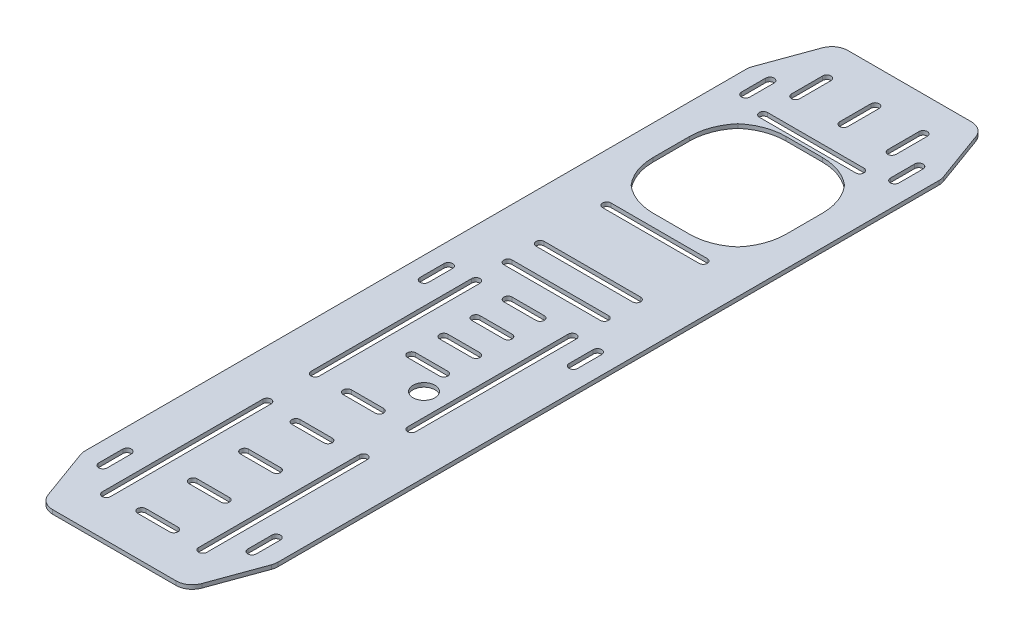
SolidWorks part; units mm, degrees
material "6061-T6 (SS)"
ref_plane "Front Plane" through (0, 0, 0) normal (0, 0, 1) x (1, 0, 0)
ref_plane "Top Plane" through (0, 0, 0) normal (0, 1, 0) x (1, 0, 0)
ref_plane "Right Plane" through (0, 0, 0) normal (1, 0, 0) x (0, 0, -1)
sketch "Sketch1" plane through (0, 0, 0) normal (0, 1, 0) x (1, 0, 0)
  line L0 (0, 495.0997) -> (0, -495.0997) construction
  line L8 (76.2, 330.2) -> (-76.2, 330.2)
  line L9 (76.2, 330.2) -> (76.2, -330.2)
  line L10 (76.2, -330.2) -> (-76.2, -330.2)
  line L11 (-76.2, 330.2) -> (-76.2, -330.2)
  line L12 (76.2, 330.2) -> (-76.2, -330.2) construction
  line L13 (76.2, -330.2) -> (-76.2, 330.2) construction
  point P7 (0, 0)
  dimension "D1" = 660.4
  dimension "D2" = 152.4
extrude "Boss-Extrude1" add sketch "Sketch1" along normal blind 3.18
sketch "Sketch5" plane through (0, 0, 0) normal (0, -1, 0) x (1, 0, 0)
  line L0 (76.2, 279.4) -> (57.7103, 330.2)
  line L1 (76.2, 330.2) -> (76.2, -330.2) construction
  line L2 (-76.2, 330.2) -> (76.2, 330.2) construction
  line L3 (57.7103, 330.2) -> (76.2, 330.2)
  line L4 (76.2, 330.2) -> (76.2, 279.4)
  line L5 (0, -1.749) -> (0, 1.749) construction
  line L6 (-57.7103, 330.2) -> (-76.2, 330.2)
  line L7 (-76.2, 279.4) -> (-57.7103, 330.2)
  line L8 (-76.2, 330.2) -> (-76.2, 279.4)
  line L9 (1.749, 0) -> (-1.749, 0) construction
  line L10 (-76.2, -279.4) -> (-57.7103, -330.2)
  line L11 (-76.2, -330.2) -> (-76.2, -279.4)
  line L12 (-57.7103, -330.2) -> (-76.2, -330.2)
  line L13 (57.7103, -330.2) -> (76.2, -330.2)
  line L14 (76.2, -279.4) -> (57.7103, -330.2)
  line L15 (76.2, -330.2) -> (76.2, -279.4)
  dimension "D1" = 20
  dimension "D2" = 50.8
sketch "Sketch3" plane through (0, 3.18, 0) normal (0, 1, 0) x (1, 0, 0)
  line L0 (-38.1, -101.6) -> (38.1, -101.6) construction
  line L1 (-76.2, -330.2) -> (76.2, -330.2) construction
  line L2 (-38.1, 50.8) -> (38.1, 50.8) construction
  line L5 (-38.1, 54.0639) -> (38.1, 54.0639)
  line L9 (-38.1, 47.5361) -> (38.1, 47.5361)
  line L12 (-76.2, 0) -> (76.2, 0) construction
  line L13 (-76.2, 330.2) -> (-76.2, -330.2) construction
  line L14 (76.2, -330.2) -> (76.2, 330.2) construction
  line L15 (-38.1, 25.4) -> (-38.1, -101.6) construction
  line L16 (-41.3639, 25.4) -> (-41.3639, -101.6)
  line L17 (-34.8361, 25.4) -> (-34.8361, -101.6)
  line L18 (38.1, 25.4) -> (38.1, -101.6) construction
  line L19 (41.3639, 25.4) -> (41.3639, -101.6)
  line L20 (34.8361, 25.4) -> (34.8361, -101.6)
  line L21 (-76.2, -38.1) -> (76.2, -38.1) construction
  line L22 (-76.2, 330.2) -> (-76.2, -330.2) construction
  line L23 (76.2, -330.2) -> (76.2, 330.2) construction
  line L24 (-38.1, -127) -> (38.1, -127) construction
  line L25 (-38.1, -130.2639) -> (38.1, -130.2639)
  line L26 (-38.1, -123.7361) -> (38.1, -123.7361)
  line L27 (-76.2, -127) -> (76.2, -127) construction
  line L28 (38.1, -279.4) -> (38.1, -152.4) construction
  line L29 (41.3639, -279.4) -> (41.3639, -152.4)
  line L30 (34.8361, -279.4) -> (34.8361, -152.4)
  line L31 (-38.1, -279.4) -> (-38.1, -152.4) construction
  line L32 (-41.3639, -279.4) -> (-41.3639, -152.4)
  line L33 (-34.8361, -279.4) -> (-34.8361, -152.4)
  line L34 (-76.2, -215.9) -> (76.2, -215.9) construction
  line L35 (-38.1, -304.8) -> (38.1, -304.8) construction
  line L36 (-38.1, -301.5361) -> (38.1, -301.5361)
  line L37 (-38.1, -308.0639) -> (38.1, -308.0639)
  line L38 (-12.7, -279.4) -> (12.7, -279.4) construction
  line L39 (-12.7, -276.1361) -> (12.7, -276.1361)
  line L40 (-12.7, -282.6639) -> (12.7, -282.6639)
  line L44 (-12.7, -228.6) -> (12.7, -228.6) construction
  line L45 (-12.7, -225.3361) -> (12.7, -225.3361)
  line L46 (-12.7, -231.8639) -> (12.7, -231.8639)
  line L47 (-12.7, -203.2) -> (12.7, -203.2) construction
  line L48 (-12.7, -199.9361) -> (12.7, -199.9361)
  line L49 (-12.7, -206.4639) -> (12.7, -206.4639)
  line L50 (-12.7, -177.8) -> (12.7, -177.8) construction
  line L51 (-12.7, -174.5361) -> (12.7, -174.5361)
  line L52 (-12.7, -181.0639) -> (12.7, -181.0639)
  line L53 (-12.7, -152.4) -> (12.7, -152.4) construction
  line L54 (-12.7, -149.1361) -> (12.7, -149.1361)
  line L55 (-12.7, -155.6639) -> (12.7, -155.6639)
  line L56 (-12.7, 25.4) -> (12.7, 25.4) construction
  line L57 (-12.7, 22.1361) -> (12.7, 22.1361)
  line L58 (-12.7, 28.6639) -> (12.7, 28.6639)
  line L59 (-12.7, 0) -> (12.7, 0) construction
  line L60 (-12.7, -3.2639) -> (12.7, -3.2639)
  line L61 (-12.7, 3.2639) -> (12.7, 3.2639)
  line L62 (-12.7, -25.4) -> (12.7, -25.4) construction
  line L63 (-12.7, -28.6639) -> (12.7, -28.6639)
  line L64 (-12.7, -22.1361) -> (12.7, -22.1361)
  line L65 (-12.7, -50.8) -> (12.7, -50.8) construction
  line L66 (-12.7, -54.0639) -> (12.7, -54.0639)
  line L67 (-12.7, -47.5361) -> (12.7, -47.5361)
  line L71 (-12.7, -101.6) -> (12.7, -101.6) construction
  line L72 (-12.7, -104.8639) -> (12.7, -104.8639)
  line L73 (-12.7, -98.3361) -> (12.7, -98.3361)
  line L74 (-76.2, 63.5) -> (76.2, 63.5) construction
  line L75 (-38.1, 76.2) -> (38.1, 76.2) construction
  line L76 (-38.1, 72.9361) -> (38.1, 72.9361)
  line L77 (-38.1, 79.4639) -> (38.1, 79.4639)
  line L78 (-76.2, 151.7678) -> (76.2, 151.7678) construction
  line L79 (76.2, 330.2) -> (-76.2, 330.2) construction
  line L80 (-38.1, 207.0156) -> (38.1, 207.0156) construction
  line L83 (-38.1, 252.7356) -> (38.1, 252.7356) construction
  line L84 (-38.1, 249.4717) -> (38.1, 249.4717)
  line L85 (-38.1, 255.9995) -> (38.1, 255.9995)
  line L86 (-38.1, 302.8393) -> (-38.1, 278.1356) construction
  line L87 (-34.8361, 302.8393) -> (-34.8361, 278.1356)
  line L88 (-41.3639, 302.8393) -> (-41.3639, 278.1356)
  line L89 (0, 302.8393) -> (0, 278.1356) construction
  line L90 (3.2639, 302.8393) -> (3.2639, 278.1356)
  line L91 (-3.2639, 302.8393) -> (-3.2639, 278.1356)
  line L92 (38.1, 302.8393) -> (38.1, 278.1356) construction
  line L93 (41.3639, 302.8393) -> (41.3639, 278.1356)
  line L94 (34.8361, 302.8393) -> (34.8361, 278.1356)
  line L95 (-38.1, 203.7517) -> (38.1, 203.7517)
  line L96 (-38.1, 210.2795) -> (38.1, 210.2795)
  line L97 (76.2, 330.2) -> (-76.2, 330.2) construction
  line L113 (-12.7, -254) -> (12.7, -254) construction
  line L114 (-12.7, -250.7361) -> (12.7, -250.7361)
  line L115 (-12.7, -257.2639) -> (12.7, -257.2639)
  line L116 (-12.7, -254) -> (12.7, -254) construction
  line L117 (-12.7, -250.7361) -> (12.7, -250.7361)
  line L118 (-12.7, -257.2639) -> (12.7, -257.2639)
  arc A4 (-41.3639, 25.4) -> (-34.8361, 25.4) centre (-38.1, 25.4) cw
  arc A5 (-34.8361, -101.6) -> (-41.3639, -101.6) centre (-38.1, -101.6) cw
  arc A6 (41.3639, 25.4) -> (34.8361, 25.4) centre (38.1, 25.4) ccw
  arc A7 (34.8361, -101.6) -> (41.3639, -101.6) centre (38.1, -101.6) ccw
  arc A8 (-38.1, 54.0639) -> (-38.1, 47.5361) centre (-38.1, 50.8) ccw
  arc A9 (38.1, 47.5361) -> (38.1, 54.0639) centre (38.1, 50.8) ccw
  arc A10 (-38.1, -130.2639) -> (-38.1, -123.7361) centre (-38.1, -127) cw
  arc A11 (38.1, -123.7361) -> (38.1, -130.2639) centre (38.1, -127) cw
  arc A12 (41.3639, -279.4) -> (34.8361, -279.4) centre (38.1, -279.4) cw
  arc A13 (34.8361, -152.4) -> (41.3639, -152.4) centre (38.1, -152.4) cw
  arc A14 (-41.3639, -279.4) -> (-34.8361, -279.4) centre (-38.1, -279.4) ccw
  arc A15 (-34.8361, -152.4) -> (-41.3639, -152.4) centre (-38.1, -152.4) ccw
  arc A16 (-38.1, -301.5361) -> (-38.1, -308.0639) centre (-38.1, -304.8) ccw
  arc A17 (38.1, -308.0639) -> (38.1, -301.5361) centre (38.1, -304.8) ccw
  arc A18 (-12.7, -276.1361) -> (-12.7, -282.6639) centre (-12.7, -279.4) ccw
  arc A19 (12.7, -282.6639) -> (12.7, -276.1361) centre (12.7, -279.4) ccw
  arc A22 (-12.7, -225.3361) -> (-12.7, -231.8639) centre (-12.7, -228.6) ccw
  arc A23 (12.7, -231.8639) -> (12.7, -225.3361) centre (12.7, -228.6) ccw
  arc A24 (-12.7, -199.9361) -> (-12.7, -206.4639) centre (-12.7, -203.2) ccw
  arc A25 (12.7, -206.4639) -> (12.7, -199.9361) centre (12.7, -203.2) ccw
  arc A26 (-12.7, -174.5361) -> (-12.7, -181.0639) centre (-12.7, -177.8) ccw
  arc A27 (12.7, -181.0639) -> (12.7, -174.5361) centre (12.7, -177.8) ccw
  arc A28 (-12.7, -149.1361) -> (-12.7, -155.6639) centre (-12.7, -152.4) ccw
  arc A29 (12.7, -155.6639) -> (12.7, -149.1361) centre (12.7, -152.4) ccw
  arc A30 (-12.7, 22.1361) -> (-12.7, 28.6639) centre (-12.7, 25.4) cw
  arc A31 (12.7, 28.6639) -> (12.7, 22.1361) centre (12.7, 25.4) cw
  arc A32 (-12.7, -3.2639) -> (-12.7, 3.2639) centre (-12.7, 0) cw
  arc A33 (12.7, 3.2639) -> (12.7, -3.2639) centre (12.7, 0) cw
  arc A34 (-12.7, -28.6639) -> (-12.7, -22.1361) centre (-12.7, -25.4) cw
  arc A35 (12.7, -22.1361) -> (12.7, -28.6639) centre (12.7, -25.4) cw
  arc A36 (-12.7, -54.0639) -> (-12.7, -47.5361) centre (-12.7, -50.8) cw
  arc A37 (12.7, -47.5361) -> (12.7, -54.0639) centre (12.7, -50.8) cw
  arc A40 (-12.7, -104.8639) -> (-12.7, -98.3361) centre (-12.7, -101.6) cw
  arc A41 (12.7, -98.3361) -> (12.7, -104.8639) centre (12.7, -101.6) cw
  arc A42 (-38.1, 72.9361) -> (-38.1, 79.4639) centre (-38.1, 76.2) cw
  arc A43 (38.1, 79.4639) -> (38.1, 72.9361) centre (38.1, 76.2) cw
  arc A46 (-38.1, 249.4717) -> (-38.1, 255.9995) centre (-38.1, 252.7356) cw
  arc A47 (38.1, 255.9995) -> (38.1, 249.4717) centre (38.1, 252.7356) cw
  arc A48 (-34.8361, 302.8393) -> (-41.3639, 302.8393) centre (-38.1, 302.8393) ccw
  arc A49 (-41.3639, 278.1356) -> (-34.8361, 278.1356) centre (-38.1, 278.1356) ccw
  arc A50 (3.2639, 302.8393) -> (-3.2639, 302.8393) centre (0, 302.8393) ccw
  arc A51 (-3.2639, 278.1356) -> (3.2639, 278.1356) centre (0, 278.1356) ccw
  arc A52 (41.3639, 302.8393) -> (34.8361, 302.8393) centre (38.1, 302.8393) ccw
  arc A53 (34.8361, 278.1356) -> (41.3639, 278.1356) centre (38.1, 278.1356) ccw
  arc A54 (-38.1, 203.7517) -> (-38.1, 210.2795) centre (-38.1, 207.0156) cw
  arc A55 (38.1, 210.2795) -> (38.1, 203.7517) centre (38.1, 207.0156) cw
  arc A68 (-12.7, -250.7361) -> (-12.7, -257.2639) centre (-12.7, -254) ccw
  arc A69 (12.7, -257.2639) -> (12.7, -250.7361) centre (12.7, -254) ccw
  point P2 (0, 50.8)
  point P26 (0, -127)
  point P36 (-38.1, -38.1)
  point P43 (38.1, -38.1)
  point P55 (38.1, -215.9)
  point P62 (-38.1, -215.9)
  point P71 (0, -304.8)
  point P78 (0, -279.4)
  point P94 (0, -228.6)
  point P101 (0, -203.2)
  point P108 (0, -177.8)
  point P115 (0, -152.4)
  point P121 (0, 25.4)
  point P128 (0, 0)
  point P135 (0, -25.4)
  point P142 (0, -50.8)
  point P156 (0, -101.6)
  point P165 (0, 76.2)
  point P176 (0, 207.0156)
  point P177 (0, 207.0156)
  point P183 (0, 252.7356)
  point P190 (-38.1, 290.4874)
  point P197 (0, 290.4874)
  point P205 (38.1, 290.4874)
  point P212 (0, -254)
  point P221 (0, -254)
  point P228 (0, -254)
  point P235 (0, -254)
  point P242 (0, -254)
  point P249 (0, -254)
  point P256 (0, -254)
  dimension "D1" = 3.2639
  dimension "D2" = 76.2
  dimension "D5" = 3.2639
  dimension "D7" = 3.2639
  dimension "D14" = 3.2639
  dimension "D3" = 228.6
  dimension "D4" = 127
  dimension "D6" = 25.4
  dimension "D8" = 25.4
  dimension "D9" = 6
  dimension "D11" = 12.7
  dimension "D12" = 50.1037
  dimension "7.02489" = 178.4322
  dimension "D13" = 25.4
  dimension "D16" = 38.1
  dimension "D17" = 123.1844
  dimension "D15" = 3
extrude "Cut-Extrude2" cut sketch "Sketch3" against normal through all
sketch "Sketch4" plane through (0, 3.18, 0) normal (0, 1, 0) x (1, 0, 0)
  line L47 (-14.3614, 141.82) -> (14.3614, 141.82)
  line L48 (52.54, 179.9986) -> (52.54, 208.7214)
  line L49 (14.3614, 246.9) -> (-14.3614, 246.9)
  line L50 (-52.54, 208.7214) -> (-52.54, 179.9986)
  line L51 (-14.3614, 141.82) -> (14.3614, 141.82)
  line L52 (52.54, 179.9986) -> (52.54, 208.7214)
  line L53 (14.3614, 246.9) -> (-14.3614, 246.9)
  line L54 (-52.54, 208.7214) -> (-52.54, 179.9986)
  arc A93 (-42.1819, 152.1781) -> (-14.3614, 141.82) centre (-14.3614, 184.36) ccw
  arc A94 (14.3614, 141.82) -> (42.1819, 152.1781) centre (14.3614, 184.36) ccw
  arc A95 (42.1819, 152.1781) -> (52.54, 179.9986) centre (10, 179.9986) ccw
  arc A96 (52.54, 208.7214) -> (42.1819, 236.5419) centre (10, 208.7214) ccw
  arc A97 (42.1819, 236.5419) -> (14.3614, 246.9) centre (14.3614, 204.36) ccw
  arc A98 (-14.3614, 246.9) -> (-42.1819, 236.5419) centre (-14.3614, 204.36) ccw
  arc A99 (-42.1819, 236.5419) -> (-52.54, 208.7214) centre (-10, 208.7214) ccw
  arc A100 (-52.54, 179.9986) -> (-42.1819, 152.1781) centre (-10, 179.9986) ccw
  arc A101 (-42.1819, 152.1781) -> (-14.3614, 141.82) centre (-14.3614, 184.36) ccw
  arc A102 (14.3614, 141.82) -> (42.1819, 152.1781) centre (14.3614, 184.36) ccw
  arc A103 (42.1819, 152.1781) -> (52.54, 179.9986) centre (10, 179.9986) ccw
  arc A104 (52.54, 208.7214) -> (42.1819, 236.5419) centre (10, 208.7214) ccw
  arc A105 (42.1819, 236.5419) -> (14.3614, 246.9) centre (14.3614, 204.36) ccw
  arc A106 (-14.3614, 246.9) -> (-42.1819, 236.5419) centre (-14.3614, 204.36) ccw
  arc A107 (-42.1819, 236.5419) -> (-52.54, 208.7214) centre (-10, 208.7214) ccw
  arc A108 (-52.54, 179.9986) -> (-42.1819, 152.1781) centre (-10, 179.9986) ccw
  dimension "D1" = 2.54
extrude "Cut-Extrude3" cut sketch "Sketch4" against normal through all
extrude "Cut-Extrude4" cut sketch "Sketch5" against normal through all
fillet "Fillet1" radius 12.7 8 edges at (-76.2, 1.59, -279.4) (-57.7103, 1.59, -330.2) (57.7103, 1.59, -330.2) (76.2, 1.59, -279.4) (76.2, 1.59, 279.4) (57.7103, 1.59, 330.2) (-57.7103, 1.59, 330.2) (-76.2, 1.59, 279.4)
sketch "Sketch6" plane through (0, 3.18, 0) normal (0, 1, 0) x (1, 0, 0)
  circle A1 centre (17.106, -70.8034) radius 8.636 construction
  circle A2 centre (17.106, -70.8034) radius 8.636
sketch "Sketch7" plane through (0, 0, 0) normal (0, -1, 0) x (1, 0, 0)
  line L0 (76.2, 330.2) -> (76.2, 120.65)
  line L1 (76.2, 277.1606) -> (76.2, -277.1606) construction
  line L2 (76.2, 120.65) -> (-76.2, 120.65)
  line L3 (-76.2, 120.65) -> (-76.2, 330.2)
  line L4 (-76.2, -277.1606) -> (-76.2, 277.1606) construction
  line L5 (-76.2, 330.2) -> (76.2, 330.2)
  line L6 (-48.8177, 330.2) -> (48.8177, 330.2) construction
  dimension "D1" = 209.55
extrude "Cut-Extrude6" cut sketch "Sketch7" against normal up to next
sketch "Sketch8" plane through (0, 0, 0) normal (0, -1, 0) x (1, 0, 0)
  line L0 (76.2, 69.85) -> (76.2, 120.65)
  line L1 (76.2, 120.65) -> (76.2, -277.1606) construction
  line L2 (76.2, 120.65) -> (57.7103, 120.65)
  line L3 (-76.2, 120.65) -> (76.2, 120.65) construction
  line L4 (57.7103, 120.65) -> (76.2, 69.85)
  line L5 (0, -330.2) -> (0, 120.65) construction
  line L6 (48.8177, -330.2) -> (-48.8177, -330.2) construction
  line L7 (-76.2, 120.65) -> (-57.7103, 120.65)
  line L8 (-76.2, 69.85) -> (-76.2, 120.65)
  line L9 (-57.7103, 120.65) -> (-76.2, 69.85)
  dimension "D1" = 50.8
  dimension "D2" = 20
sketch "Sketch9" plane through (0, 0, 0) normal (0, -1, 0) x (1, 0, 0)
  line L0 (58.674, -259.715) -> (58.674, -278.765) construction
  line L1 (62.0522, -259.715) -> (62.0522, -278.765)
  line L2 (55.2958, -259.715) -> (55.2958, -278.765)
  line L3 (-59.0358, -259.715) -> (-59.0358, -278.765) construction
  line L4 (-55.6576, -259.715) -> (-55.6576, -278.765)
  line L5 (-62.414, -259.715) -> (-62.414, -278.765)
  line L6 (-59.182, -259.715) -> (-59.182, -278.765) construction
  line L7 (76.2, 120.65) -> (76.2, -277.1606) construction
  line L8 (-76.2, -277.1606) -> (-76.2, 120.65) construction
  line L9 (-55.8038, -259.715) -> (-55.8038, -278.765)
  line L15 (58.674, -269.24) -> (-59.0358, -269.24) construction
  line L16 (48.8177, -330.2) -> (-48.8177, -330.2) construction
  line L18 (-62.5602, -259.715) -> (-62.5602, -278.765)
  line L21 (0, 120.65) -> (0, 171.45) construction
  line L22 (0, -330.2) -> (0, 171.45) construction
  line L23 (-59.182, -5.715) -> (-59.182, -24.765) construction
  line L24 (-55.8038, -5.715) -> (-55.8038, -24.765)
  line L25 (-62.5602, -5.715) -> (-62.5602, -24.765)
  line L26 (-59.182, 248.285) -> (-59.182, 229.235) construction
  line L27 (-55.8038, 248.285) -> (-55.8038, 229.235)
  line L28 (-62.5602, 248.285) -> (-62.5602, 229.235)
  line L29 (58.674, -5.715) -> (58.674, -24.765) construction
  line L30 (62.0522, -5.715) -> (62.0522, -24.765)
  line L31 (55.2958, -5.715) -> (55.2958, -24.765)
  line L32 (58.674, 248.285) -> (58.674, 229.235) construction
  line L33 (62.0522, 248.285) -> (62.0522, 229.235)
  line L34 (55.2958, 248.285) -> (55.2958, 229.235)
  arc A0 (62.0522, -259.715) -> (55.2958, -259.715) centre (58.674, -259.715) ccw
  arc A1 (55.2958, -278.765) -> (62.0522, -278.765) centre (58.674, -278.765) ccw
  arc A3 (-55.6576, -259.715) -> (-62.414, -259.715) centre (-59.0358, -259.715) ccw
  arc A4 (-62.414, -278.765) -> (-55.6576, -278.765) centre (-59.0358, -278.765) ccw
  arc A12 (-55.8038, -259.715) -> (-62.5602, -259.715) centre (-59.182, -259.715) ccw
  arc A13 (-62.5602, -278.765) -> (-55.8038, -278.765) centre (-59.182, -278.765) ccw
  arc A14 (-55.8038, -5.715) -> (-62.5602, -5.715) centre (-59.182, -5.715) ccw
  arc A15 (-62.5602, -24.765) -> (-55.8038, -24.765) centre (-59.182, -24.765) ccw
  arc A16 (-55.8038, 248.285) -> (-62.5602, 248.285) centre (-59.182, 248.285) ccw
  arc A17 (-62.5602, 229.235) -> (-55.8038, 229.235) centre (-59.182, 229.235) ccw
  arc A18 (62.0522, -5.715) -> (55.2958, -5.715) centre (58.674, -5.715) ccw
  arc A19 (55.2958, -24.765) -> (62.0522, -24.765) centre (58.674, -24.765) ccw
  arc A20 (62.0522, 248.285) -> (55.2958, 248.285) centre (58.674, 248.285) ccw
  arc A21 (55.2958, 229.235) -> (62.0522, 229.235) centre (58.674, 229.235) ccw
  point P3 (58.674, -269.24)
  point P13 (-59.0358, -269.24)
  point P19 (0, 0)
  point P20 (0, 0)
  point P21 (0, 0)
  point P28 (-59.182, -269.24)
  point P35 (-59.182, -15.24)
  point P42 (-59.182, 238.76)
  point P54 (58.674, -15.24)
  point P61 (58.674, 238.76)
  point P66 (0, 0)
  point P67 (0, 0)
  dimension "D2" = 3.3782
  dimension "D1" = 19.05
  dimension "D3" = 60.96
  dimension "D4" = 17.1642
  dimension "D5" = 17.526
  dimension "D6" = 50.8
  dimension "D7" = 2
  dimension "D8" = 3
extrude "Cut-Extrude9" cut sketch "Sketch6" against normal through all
sketch "Sketch10" plane through (0, 0, 0) normal (0, -1, 0) x (1, 0, 0)
  line L0 (-38.1, -252.7356) -> (-38.1, -103.0796) construction
  line L3 (38.1, -252.7356) -> (38.1, -103.0796) construction
  line L4 (-38.1, -128.9041) -> (38.1, -128.9041) construction
  line L5 (-38.1, -128.9041) -> (38.1, -128.9041) construction
  line L6 (-38.1, -125.6402) -> (38.1, -125.6402)
  line L7 (-38.1, -132.168) -> (38.1, -132.168)
  line L8 (-14.3614, -141.82) -> (14.3614, -141.82) construction
  arc A2 (-38.1, -125.6402) -> (-38.1, -132.168) centre (-38.1, -128.9041) ccw
  arc A3 (38.1, -132.168) -> (38.1, -125.6402) centre (38.1, -128.9041) ccw
  arc A4 (-38.1, -249.4717) -> (-38.1, -255.9995) centre (-38.1, -252.7356) ccw construction
  point P4 (-0.038, -128.9041)
  point P9 (0, -128.9041)
  dimension "D1" = 9.652
extrude "Cut-Extrude10" cut sketch "Sketch10" against normal through all
sketch "Sketch11" plane through (0, 0, 120.65) normal (0, 0, 1) x (1, 0, 0)
  line L0 (-75.4341, 3.18) -> (76.2, 3.18)
  line L1 (76.2, 3.18) -> (76.2, 0)
  line L2 (76.2, 0) -> (-76.2, 0)
  line L3 (-76.2, 0) -> (-76.2, 3.18)
  line L4 (-76.2, 3.18) -> (-75.4341, 3.18)
extrude "Boss-Extrude2" add sketch "Sketch11" along normal blind 177.8
sketch "Sketch12" plane through (0, 0, 0) normal (0, -1, 0) x (1, 0, 0)
  line L0 (76.2, 298.45) -> (76.2, 247.65)
  line L1 (76.2, 298.45) -> (76.2, -277.1606) construction
  line L2 (76.2, 247.65) -> (57.7103, 298.45)
  line L3 (-76.2, 298.45) -> (76.2, 298.45) construction
  line L4 (57.7103, 298.45) -> (76.2, 298.45)
  line L5 (-76.2, 298.45) -> (-76.2, 247.65)
  line L6 (-76.2, -277.1606) -> (-76.2, 298.45) construction
  line L7 (-76.2, 247.65) -> (-57.7103, 298.45)
  line L8 (-57.7103, 298.45) -> (-76.2, 298.45)
  dimension "D1" = 20
  dimension "D2" = 50.8
  dimension "D3" = 20
  dimension "D4" = 50.8
extrude "Cut-Extrude11" cut sketch "Sketch12" against normal blind 177.8
fillet "Fillet2" radius 12.7 4 edges at (-57.7103, 1.59, 298.45) (-76.2, 1.59, 247.65) (57.7103, 1.59, 298.45) (76.2, 1.59, 247.65)
sketch "Sketch13" plane through (0, 0, 0) normal (0, -1, 0) x (1, 0, 0)
  line L0 (-55.8038, 248.285) -> (-55.8038, 229.235) construction
  line L1 (-55.8038, 248.285) -> (-55.8038, 229.235)
  line L2 (62.0522, -259.715) -> (62.0522, -278.765) construction
  line L3 (-62.414, -259.715) -> (-62.414, -278.765) construction
  line L4 (-55.8038, -5.715) -> (-55.8038, -24.765) construction
  line L5 (62.0522, -5.715) -> (62.0522, -24.765) construction
  line L6 (55.2958, 248.285) -> (55.2958, 229.235) construction
  line L7 (62.0522, -259.715) -> (62.0522, -278.765)
  line L8 (-62.414, -259.715) -> (-62.414, -278.765)
  line L9 (-55.8038, -5.715) -> (-55.8038, -24.765)
  line L10 (62.0522, -5.715) -> (62.0522, -24.765)
  line L11 (55.2958, 248.285) -> (55.2958, 229.235)
  line L12 (55.2958, -259.715) -> (55.2958, -278.765) construction
  line L13 (-55.6576, -259.715) -> (-55.6576, -278.765) construction
  line L14 (-62.5602, -5.715) -> (-62.5602, -24.765) construction
  line L15 (55.2958, -5.715) -> (55.2958, -24.765) construction
  line L16 (-62.5602, 248.285) -> (-62.5602, 229.235) construction
  line L17 (55.2958, -259.715) -> (55.2958, -278.765)
  line L18 (-55.6576, -259.715) -> (-55.6576, -278.765)
  line L19 (-62.5602, -5.715) -> (-62.5602, -24.765)
  line L20 (55.2958, -5.715) -> (55.2958, -24.765)
  line L21 (-62.5602, 248.285) -> (-62.5602, 229.235)
  line L22 (62.0522, 248.285) -> (62.0522, 229.235) construction
  line L23 (62.0522, 248.285) -> (62.0522, 229.235)
  arc A0 (-55.8038, 248.285) -> (-62.5602, 248.285) centre (-59.182, 248.285) ccw construction
  arc A1 (-55.8038, 248.285) -> (-62.5602, 248.285) centre (-59.182, 248.285) ccw
  arc A2 (55.2958, -278.765) -> (62.0522, -278.765) centre (58.674, -278.765) ccw construction
  arc A3 (62.0522, -259.715) -> (55.2958, -259.715) centre (58.674, -259.715) ccw construction
  arc A4 (-55.6576, -259.715) -> (-62.414, -259.715) centre (-59.0358, -259.715) ccw construction
  arc A5 (-62.414, -278.765) -> (-55.6576, -278.765) centre (-59.0358, -278.765) ccw construction
  arc A6 (-55.8038, -5.715) -> (-62.5602, -5.715) centre (-59.182, -5.715) ccw construction
  arc A7 (-62.5602, -24.765) -> (-55.8038, -24.765) centre (-59.182, -24.765) ccw construction
  arc A8 (62.0522, -5.715) -> (55.2958, -5.715) centre (58.674, -5.715) ccw construction
  arc A9 (55.2958, -24.765) -> (62.0522, -24.765) centre (58.674, -24.765) ccw construction
  arc A10 (62.0522, 248.285) -> (55.2958, 248.285) centre (58.674, 248.285) ccw construction
  arc A11 (55.2958, 229.235) -> (62.0522, 229.235) centre (58.674, 229.235) ccw construction
  arc A12 (-62.5602, 229.235) -> (-55.8038, 229.235) centre (-59.182, 229.235) ccw construction
  arc A13 (55.2958, -278.765) -> (62.0522, -278.765) centre (58.674, -278.765) ccw
  arc A14 (62.0522, -259.715) -> (55.2958, -259.715) centre (58.674, -259.715) ccw
  arc A15 (-55.6576, -259.715) -> (-62.414, -259.715) centre (-59.0358, -259.715) ccw
  arc A16 (-62.414, -278.765) -> (-55.6576, -278.765) centre (-59.0358, -278.765) ccw
  arc A17 (-55.8038, -5.715) -> (-62.5602, -5.715) centre (-59.182, -5.715) ccw
  arc A18 (-62.5602, -24.765) -> (-55.8038, -24.765) centre (-59.182, -24.765) ccw
  arc A19 (62.0522, -5.715) -> (55.2958, -5.715) centre (58.674, -5.715) ccw
  arc A20 (55.2958, -24.765) -> (62.0522, -24.765) centre (58.674, -24.765) ccw
  arc A21 (62.0522, 248.285) -> (55.2958, 248.285) centre (58.674, 248.285) ccw
  arc A22 (55.2958, 229.235) -> (62.0522, 229.235) centre (58.674, 229.235) ccw
  arc A23 (-62.5602, 229.235) -> (-55.8038, 229.235) centre (-59.182, 229.235) ccw
  point P0 (58.674, 248.285)
  point P2 (0, 0)
extrude "Cut-Extrude12" cut sketch "Sketch13" against normal blind 177.8
ref_plane "Plane1" through (34.8361, 0, -25.4) normal (0, 0, 1) x (1, 0, 0)
sketch "Sketch15" plane through (0, 3.18, 0) normal (0, 1, 0) x (1, 0, 0)
  line L0 (-34.8361, -101.6) -> (-34.8361, 25.4) construction
  line L1 (-41.3639, 25.4) -> (-41.3639, -101.6) construction
  line L2 (-34.8361, -101.6) -> (-34.8361, 25.4)
  line L3 (-41.3639, 25.4) -> (-41.3639, -101.6)
  line L4 (34.8361, 25.4) -> (34.8361, -101.6)
  line L5 (41.3639, -101.6) -> (41.3639, 25.4)
  line L6 (34.8361, -139.7) -> (34.8361, -266.7)
  line L7 (41.3639, -266.7) -> (41.3639, -139.7)
  line L8 (-41.3639, -139.7) -> (-41.3639, -266.7)
  line L9 (-34.8361, -266.7) -> (-34.8361, -139.7)
  arc A0 (-34.8361, 25.4) -> (-41.3639, 25.4) centre (-38.1, 25.4) ccw construction
  arc A1 (-41.3639, -101.6) -> (-34.8361, -101.6) centre (-38.1, -101.6) ccw construction
  arc A2 (-34.8361, 25.4) -> (-41.3639, 25.4) centre (-38.1, 25.4) ccw
  arc A3 (-41.3639, -101.6) -> (-34.8361, -101.6) centre (-38.1, -101.6) ccw
  arc A4 (41.3639, 25.4) -> (34.8361, 25.4) centre (38.1, 25.4) ccw
  arc A5 (34.8361, -101.6) -> (41.3639, -101.6) centre (38.1, -101.6) ccw
  arc A6 (41.3639, -139.7) -> (34.8361, -139.7) centre (38.1, -139.7) ccw
  arc A7 (34.8361, -266.7) -> (41.3639, -266.7) centre (38.1, -266.7) ccw
  arc A8 (-34.8361, -139.7) -> (-41.3639, -139.7) centre (-38.1, -139.7) ccw
  arc A9 (-41.3639, -266.7) -> (-34.8361, -266.7) centre (-38.1, -266.7) ccw
  point P4 (0, 0)
  dimension "D1" = 2
  dimension "D2" = 2
extrude "Cut-Extrude13" cut sketch "Sketch15" against normal blind 177.8
sketch "Sketch16" plane through (0, 3.18, 0) normal (0, 1, 0) x (1, 0, 0)
  line L0 (12.7, -98.3361) -> (-12.7, -98.3361) construction
  line L1 (-12.7, -104.8639) -> (12.7, -104.8639) construction
  line L2 (12.7, -98.3361) -> (-12.7, -98.3361)
  line L3 (-12.7, -104.8639) -> (12.7, -104.8639)
  line L4 (-12.7, -145.5039) -> (12.7, -145.5039)
  line L5 (12.7, -138.9761) -> (-12.7, -138.9761)
  line L6 (-12.7, -186.1439) -> (12.7, -186.1439)
  line L7 (12.7, -179.6161) -> (-12.7, -179.6161)
  line L8 (-12.7, -226.7839) -> (12.7, -226.7839)
  line L9 (12.7, -220.2561) -> (-12.7, -220.2561)
  line L10 (-12.7, -267.4239) -> (12.7, -267.4239)
  line L11 (12.7, -260.8961) -> (-12.7, -260.8961)
  arc A0 (-12.7, -98.3361) -> (-12.7, -104.8639) centre (-12.7, -101.6) ccw construction
  arc A1 (12.7, -104.8639) -> (12.7, -98.3361) centre (12.7, -101.6) ccw construction
  arc A2 (-12.7, -98.3361) -> (-12.7, -104.8639) centre (-12.7, -101.6) ccw
  arc A3 (12.7, -104.8639) -> (12.7, -98.3361) centre (12.7, -101.6) ccw
  arc A4 (-12.7, -138.9761) -> (-12.7, -145.5039) centre (-12.7, -142.24) ccw
  arc A5 (12.7, -145.5039) -> (12.7, -138.9761) centre (12.7, -142.24) ccw
  arc A6 (-12.7, -179.6161) -> (-12.7, -186.1439) centre (-12.7, -182.88) ccw
  arc A7 (12.7, -186.1439) -> (12.7, -179.6161) centre (12.7, -182.88) ccw
  arc A8 (-12.7, -220.2561) -> (-12.7, -226.7839) centre (-12.7, -223.52) ccw
  arc A9 (12.7, -226.7839) -> (12.7, -220.2561) centre (12.7, -223.52) ccw
  arc A10 (-12.7, -260.8961) -> (-12.7, -267.4239) centre (-12.7, -264.16) ccw
  arc A11 (12.7, -267.4239) -> (12.7, -260.8961) centre (12.7, -264.16) ccw
  dimension "D1" = 5
extrude "Cut-Extrude15" cut sketch "Sketch16" against normal blind 177.8
